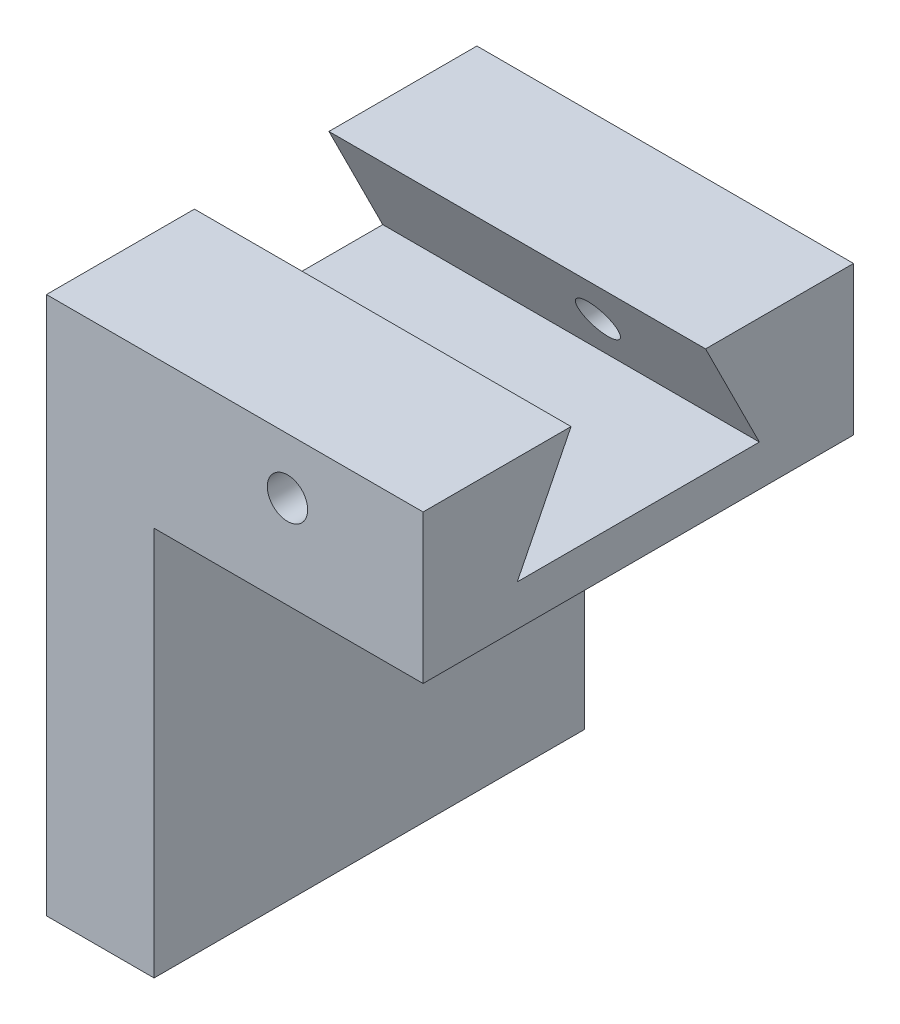
SolidWorks part; units mm, degrees
ref_plane "Front Plane" through (0, 0, 0) normal (0, 0, 1) x (1, 0, 0)
ref_plane "Top Plane" through (0, 0, 0) normal (0, 1, 0) x (1, 0, 0)
ref_plane "Right Plane" through (0, 0, 0) normal (1, 0, 0) x (0, 0, -1)
sketch "Sketch1" plane through (0, 0, 0) normal (0, 0, 1) x (1, 0, 0)
  line L0 (-9.5, -4.5) -> (-8, -4.5)
  line L1 (-9.5, -4.5) -> (9.5, -4.5)
  line L2 (-9.5, -4.5) -> (-9.5, 4.5)
  line L3 (-9.5, 4.5) -> (9.5, 4.5)
  line L4 (9.5, -4.5) -> (9.5, 4.5)
  line L5 (-9.5, -4.5) -> (9.5, 4.5) construction
  line L6 (-9.5, 4.5) -> (9.5, -4.5) construction
  line L7 (9.5, -4.5) -> (8, -4.5)
  line L8 (9.5, -4.5) -> (8, -4.5)
  line L10 (-8, -4.5) -> (8, -4.5)
  line L11 (-8, -4.5) -> (-8, 3)
  line L12 (-8, 3) -> (8, 3)
  line L13 (8, -4.5) -> (8, 3)
  point P0 (0, 0)
  dimension "D1" = 19
  dimension "D2" = 9
  dimension "D3" = 1.5
  dimension "D4" = 16
  dimension "D5" = 1.5
extrude "Boss-Extrude1" add sketch "Sketch1" along normal mid plane 8 contours L2 L1 L4 L3
sketch "Sketch2" plane through (0, 0, 4) normal (0, 0, 1) x (1, 0, 0)
  line L0 (-9.5, -4.5) -> (9.5, -4.5) construction
  line L1 (-7.5, -4.5) -> (7.5, -4.5)
  line L2 (-7.5, -4.5) -> (-7.5, 2.5)
  line L3 (-7.5, 2.5) -> (7.5, 2.5)
  line L4 (7.5, -4.5) -> (7.5, 2.5)
  line L5 (-9.5, -4.5) -> (-9.5, 4.5) construction
  line L6 (9.5, -4.5) -> (9.5, 4.5) construction
  line L7 (-9.5, 4.5) -> (9.5, 4.5) construction
  dimension "D1" = 2
  dimension "D2" = 2
  dimension "D3" = 2
extrude "Cut-Extrude1" cut sketch "Sketch2" against normal up to next
sketch "Sketch5" plane through (0, 0, 4) normal (0, 0, 1) x (1, 0, 0)
  line L5 (7.5, -4.5) -> (9.5, -4.5)
  line L6 (7.5, -4.5) -> (7.5, 4.5)
  line L7 (7.5, 4.5) -> (9.5, 4.5)
  line L8 (9.5, -4.5) -> (9.5, 4.5)
extrude "Cut-Extrude3" cut sketch "Sketch5" against normal up to next
sketch "Sketch6" plane through (-7.5, 0, 0) normal (1, 0, 0) x (0, 0, -1)
  line L1 (4, 2.5) -> (-4, 2.5) construction
  line L2 (4, 2.5) -> (-4, 2.5) construction
  line L6 (0.75, 2.5) -> (1.25, 2.5)
  line L7 (4, -4.5) -> (4, 2.5) construction
  line L8 (-4, 2.5) -> (4, 2.5)
  line L9 (-2, 1) -> (-2.25, 0.5)
  line L10 (1.25, 2.5) -> (2, 1)
  line L11 (2, 1) -> (2.25, 0.5)
  line L12 (2.25, 0.5) -> (-2.25, 0.5)
  line L13 (-1.25, 2.5) -> (1.25, 2.5)
  line L14 (2.25, 0.5) -> (1.25, 2.5)
  line L15 (-1.25, 2.5) -> (-2, 1)
  line L16 (-4, 2.5) -> (-4, -0.261)
  line L17 (-4, -0.261) -> (4, -0.261)
  line L18 (4, 2.5) -> (4, -0.261)
  line M12 (4, -4.5) -> (4, 2.5)
  line M13 (4, 2.5) -> (-4, 2.5)
  line M14 (-4, 2.5) -> (-4, -4.5)
extrude "Boss-Extrude2" add sketch "Sketch6" along normal blind 5 contours L17 L10 L11 L12 L9 L15 L8 M14 M12 M13
sketch "Sketch7" plane through (7.5, 0, 0) normal (1, 0, 0) x (0, 0, -1)
  line L1 (-4, 2.5) -> (4, 2.5)
  line L2 (-4, 2.5) -> (-4, 4.5)
  line L3 (-4, 4.5) -> (4, 4.5)
  line L4 (4, 2.5) -> (4, 4.5)
extrude "Cut-Extrude4" cut sketch "Sketch7" against normal up to next contours L2 L1 L4 L3
sketch "Sketch8" plane through (0, 0, -4) normal (0, 0, -1) x (-1, 0, 0)
  line L2 (2.5, 2.5) -> (2.5, -0.261)
  line L3 (2.5, -0.261) -> (7.5, -0.261)
  circle A0 centre (5.0199, 1.4628) radius 0.375
  dimension "D1" = 0.75
extrude "Cut-Extrude6" cut sketch "Sketch8" against normal up to surface (8 mm away) contours A0 up to face at (-6.5, -0.7537, 4)
sketch "Sketch9" plane through (0, 0, -4) normal (0, 0, -1) x (-1, 0, 0)
  line L0 (9.5, -4.5) -> (9.5, 2.5) construction
  line L1 (7.5, -0.261) -> (9.5, -0.261)
  line L2 (7.5, -0.261) -> (7.5, -7.501)
  line L3 (7.5, -7.501) -> (9.5, -7.501)
  line L4 (9.5, -0.261) -> (9.5, -7.501)
  dimension "D1" = 7.24
extrude "Boss-Extrude3" add sketch "Sketch9" against normal up to surface (8 mm away) up to face at (-4.6449, 1.4628, 4)
sketch "Sketch10" plane through (-7.5, 0, 0) normal (1, 0, 0) x (0, 0, -1)
  line L0 (-2.25, 0.5) -> (-1.25, 2.5)
  line L1 (-1.25, 2.5) -> (1.25, 2.5)
  line L2 (1.25, 2.5) -> (2.25, 0.5)
  line L3 (2.25, 0.5) -> (-2.25, 0.5)
extrude "Cut-Extrude7" cut sketch "Sketch10" against normal up to next
